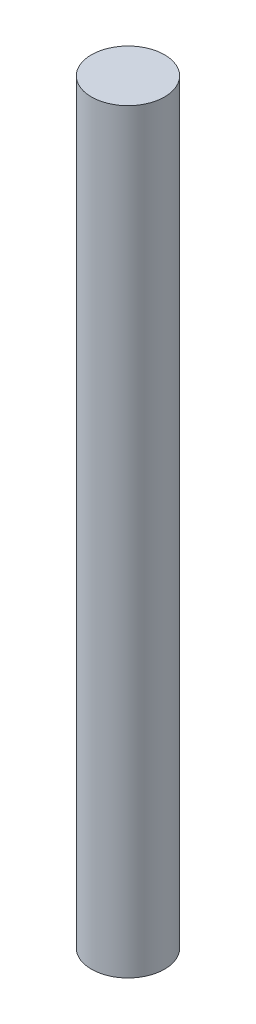
SolidWorks part; units mm, degrees
ref_plane "Front" through (0, 0, 0) normal (0, 0, 1) x (1, 0, 0)
ref_plane "Top" through (0, 0, 0) normal (0, 1, 0) x (1, 0, 0)
ref_plane "Right" through (0, 0, 0) normal (1, 0, 0) x (0, 0, -1)
sketch "Sketch1" plane through (0, 0, 0) normal (0, 1, 0) x (1, 0, 0)
  circle A0 centre (0, 0) radius 1.5
  dimension "D1" = 3
extrude "Boss-Extrude1" add sketch "Sketch1" along normal blind 31
